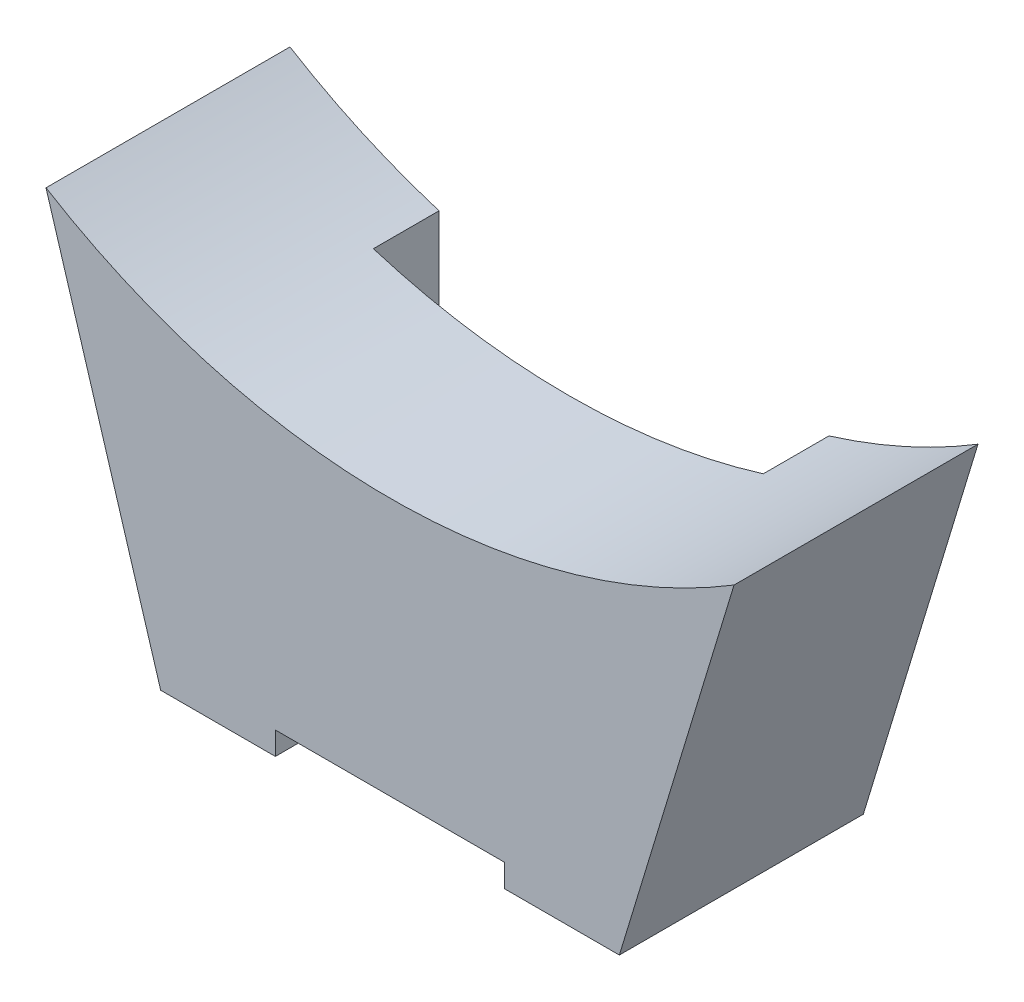
SolidWorks part; units mm, degrees
ref_plane "Plan de face" through (0, 0, 0) normal (0, 0, 1) x (1, 0, 0)
ref_plane "Plan de dessus" through (0, 0, 0) normal (0, 1, 0) x (1, 0, 0)
ref_plane "Plan de droite" through (0, 0, 0) normal (1, 0, 0) x (0, 0, -1)
sketch "Esquisse1" plane through (0, 0, 0) normal (0, 0, 1) x (1, 0, 0)
  line L0 (0, -64.5422) -> (0, -98.9751) construction
  line L1 (-15.6, -80) -> (-20, -80)
  line L2 (-20, -80) -> (-20, -60)
  line L3 (-20, -60) -> (20, -60)
  line L4 (20, -80) -> (20, -60)
  line L5 (8.8, -71.5) -> (-8.8, -71.5)
  line L6 (-8.8, -71.5) -> (-8.8, -76.5)
  line L7 (-8.8, -76.5) -> (-15.6, -76.5)
  line L8 (-15.6, -76.5) -> (-15.6, -80)
  line L9 (15.6, -80) -> (20, -80)
  line L10 (15.6, -76.5) -> (15.6, -80)
  line L11 (8.8, -76.5) -> (15.6, -76.5)
  line L12 (8.8, -71.5) -> (8.8, -76.5)
  line L13 (-15.4, -77.5) -> (-15.4, -79.8) construction
  line L14 (-8.6, -76.8) -> (-8.6, -72.6) construction
  line L15 (-15.3, -76.5) -> (-9.3, -76.5) construction
  line L16 (-7.9, -72.5) -> (7.9, -72.5) construction
  line L17 (13.9, -80) -> (-13.9, -80) construction
  point P6 (0, -71.5)
  point P17 (0, -60)
  dimension "D1" = 0.2
  dimension "D2" = 0.2
  dimension "D3" = 1
  dimension "D4" = 40
  dimension "D5" = 20
extrude "Boss.-Extru.1" add sketch "Esquisse1" along normal up to surface (18.275 mm away)
sketch "Esquisse2" plane through (0, 0, 18.275) normal (0, 0, 1) x (1, 0, 0)
  line L1 (-20, -60) -> (20, -60)
  line L2 (-20, -60) -> (-20, -82)
  line L3 (-20, -82) -> (20, -82)
  line L4 (20, -60) -> (20, -82)
  dimension "D1" = 22
extrude "Boss.-Extru.2" add sketch "Esquisse2" along normal blind 3
sketch "Esquisse3" plane through (0, 0, 18.275) normal (0, 0, -1) x (-1, 0, 0)
  line L1 (20, -80) -> (-20, -80)
  line L2 (20, -80) -> (20, -82)
  line L3 (20, -82) -> (-20, -82)
  line L4 (-20, -80) -> (-20, -82)
extrude "Boss.-Extru.3" add sketch "Esquisse3" along normal blind 2
sketch "Esquisse4" plane through (0, 0, 21.275) normal (0, 0, 1) x (1, 0, 0)
  line L0 (-20, -82) -> (20, -82) construction
  line L1 (-10, -82) -> (10, -82)
  line L2 (-10, -82) -> (-10, -80)
  line L3 (-10, -80) -> (10, -80)
  line L4 (10, -82) -> (10, -80)
  line L5 (0, -62.6461) -> (0, -87.0816) construction
  line L6 (-20, -60) -> (-20, -82) construction
  line L7 (20, -82) -> (20, -60) construction
  line L9 (15.6, -80) -> (20, -80) construction
  dimension "D1" = 20
extrude "Enlèv. mat.-Extru.2" cut sketch "Esquisse4" against normal through all
sketch "Esquisse5" plane through (0, 0, 0) normal (0, 0, -1) x (-1, 0, 0)
  line L0 (8.8, -71.5) -> (-8.8, -71.5) construction
  line L1 (15.6, -76.5) -> (-15.6, -76.5)
  line L2 (15.6, -76.5) -> (15.6, -71.5)
  line L3 (15.6, -71.5) -> (-15.6, -71.5)
  line L4 (-15.6, -76.5) -> (-15.6, -71.5)
extrude "Enlèv. mat.-Extru.3" cut sketch "Esquisse5" against normal up to surface (7.775 mm away)
sketch "Esquisse6" plane through (0, -71.5, 0) normal (0, -1, 0) x (1, 0, 0)
  line L0 (13.9, 5.725) -> (-13.9, 5.725) construction
  line L1 (-17, 5.725) -> (17, 5.725)
  line L2 (-17, 5.725) -> (-17, 0)
  line L3 (-17, 0) -> (17, 0)
  line L4 (17, 5.725) -> (17, 0)
  line L5 (-15.6, 0) -> (15.6, 0) construction
  line L6 (0, 2.4359) -> (0, -2.3605) construction
  dimension "D1" = 34
extrude "Enlèv. mat.-Extru.4" cut sketch "Esquisse6" against normal through all
sketch "Esquisse7" plane through (0, 0, 21.275) normal (0, 0, 1) x (1, 0, 0)
  line L0 (0, -113.5209) -> (0, -99.9332) construction
  line L1 (-20, -60) -> (-20, -82) construction
  line L2 (20, -82) -> (20, -60) construction
  line L3 (-30, -49.0535) -> (-20, -82)
  line L4 (20, -82) -> (30, -49.0535)
  line L5 (20, -60) -> (-20, -60) construction
  line L6 (18, -60) -> (-18, -60)
  line L7 (-18, -60) -> (-18, -82)
  line L8 (-20, -82) -> (-10, -82) construction
  line L9 (-18, -82) -> (-20, -82)
  line L10 (18, -82) -> (20, -82)
  line L11 (18, -60) -> (18, -82)
  arc A0 (-30, -49.0535) -> (30, -49.0535) centre (0, 0) ccw
  arc A1 (25.1136, -51.7258) -> (57.3526, 4.1138) centre (0, 0) ccw construction
  dimension "D1" = 60
  dimension "D2" = 2
extrude "Boss.-Extru.4" add sketch "Esquisse7" against normal up to surface (21.275 mm away) up to face at (17.5333, -70.5, 0)
sketch "Esquisse8" plane through (0, -60, 0) normal (0, -1, 0) x (1, 0, 0)
  line L4 (-17, 5.725) -> (-17, 0)
  line L5 (-17, 0) -> (17, 0)
  line L6 (17, 0) -> (17, 5.725)
  line L7 (17, 5.725) -> (-17, 5.725)
  line L8 (-17, 5.725) -> (-17, 0)
  line L9 (-17, 0) -> (17, 0)
  line L10 (17, 0) -> (17, 5.725)
  line L11 (17, 5.725) -> (-17, 5.725)
  dimension "D1" = 0
extrude "Enlèv. mat.-Extru.5" cut sketch "Esquisse8" against normal through all
